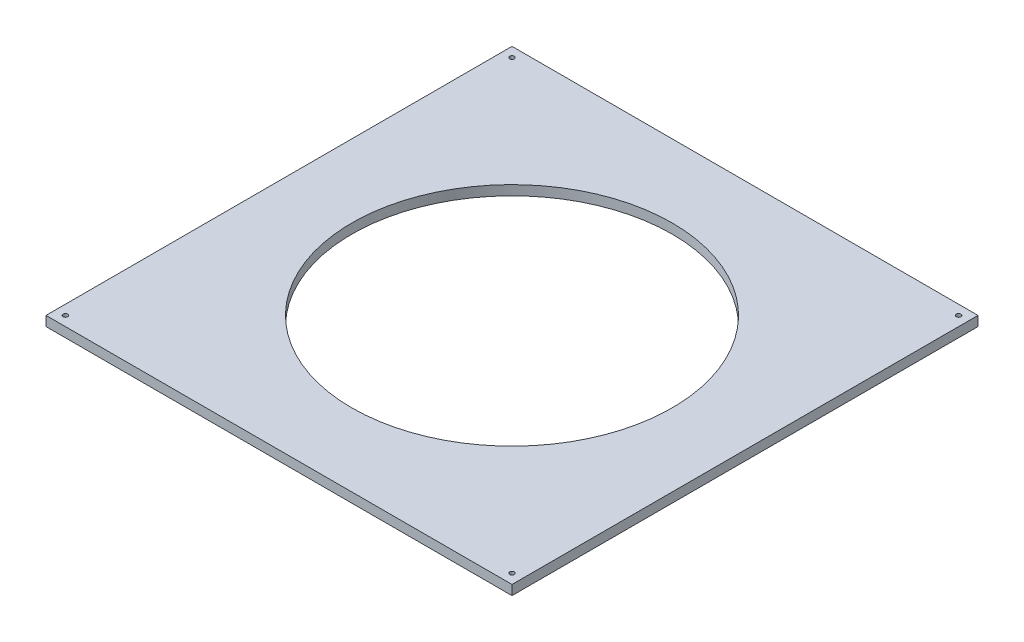
SolidWorks part; units mm, degrees
material "Pine"
ref_plane "Front Plane" through (0, 0, 0) normal (0, 0, 1) x (1, 0, 0)
ref_plane "Top Plane" through (0, 0, 0) normal (0, 1, 0) x (1, 0, 0)
ref_plane "Right Plane" through (0, 0, 0) normal (1, 0, 0) x (0, 0, -1)
sketch "Sketch1" plane through (0, 0, 0) normal (0, 1, 0) x (1, 0, 0)
  line L1 (-50.5057, 44.4593) -> (559.0943, 44.4593)
  line L2 (-50.5057, 44.4593) -> (-50.5057, -565.1407)
  line L3 (-50.5057, -565.1407) -> (559.0943, -565.1407)
  line L4 (559.0943, 44.4593) -> (559.0943, -565.1407)
  dimension "D1" = 609.6
  dimension "D2" = 609.6
extrude "Boss-Extrude1" add sketch "Sketch1" along normal blind 12.7
sketch "Sketch2" plane through (0, 12.7, 0) normal (0, 1, 0) x (1, 0, 0)
  line L0 (559.0943, 44.4593) -> (-50.5057, 44.4593) construction
  line L1 (-50.5057, 44.4593) -> (-50.5057, -565.1407) construction
  circle A0 centre (254.2943, -260.3407) radius 209.55
  dimension "D1" = 419.1
  dimension "D2" = 304.8
  dimension "D3" = 304.8
extrude "Cut-Extrude1" cut sketch "Sketch2" against normal through all
sketch "Sketch3" plane through (0, 0, 0) normal (0, -1, 0) x (1, 0, 0)
  line L0 (-50.5057, 565.1407) -> (559.0943, 565.1407) construction
  line L1 (-50.5057, -44.4593) -> (-50.5057, 565.1407) construction
  line L2 (559.0943, 565.1407) -> (559.0943, -44.4593) construction
  line L3 (559.0943, -44.4593) -> (-50.5057, -44.4593) construction
  circle A0 centre (-37.8057, 552.4407) radius 3
  circle A1 centre (546.3943, 552.4407) radius 3
  circle A2 centre (546.3943, -31.7593) radius 3
  circle A3 centre (-37.8057, -31.7593) radius 3
  dimension "D1" = 6
  dimension "D2" = 6
  dimension "D3" = 6
  dimension "D4" = 6
  dimension "D5" = 12.7
  dimension "D6" = 12.7
  dimension "D7" = 12.7
  dimension "D9" = 12.7
  dimension "D11" = 12.7
  dimension "D8" = 12.7
  dimension "D10" = 12.7
  dimension "D12" = 12.7
extrude "Cut-Extrude2" cut sketch "Sketch3" against normal through all
